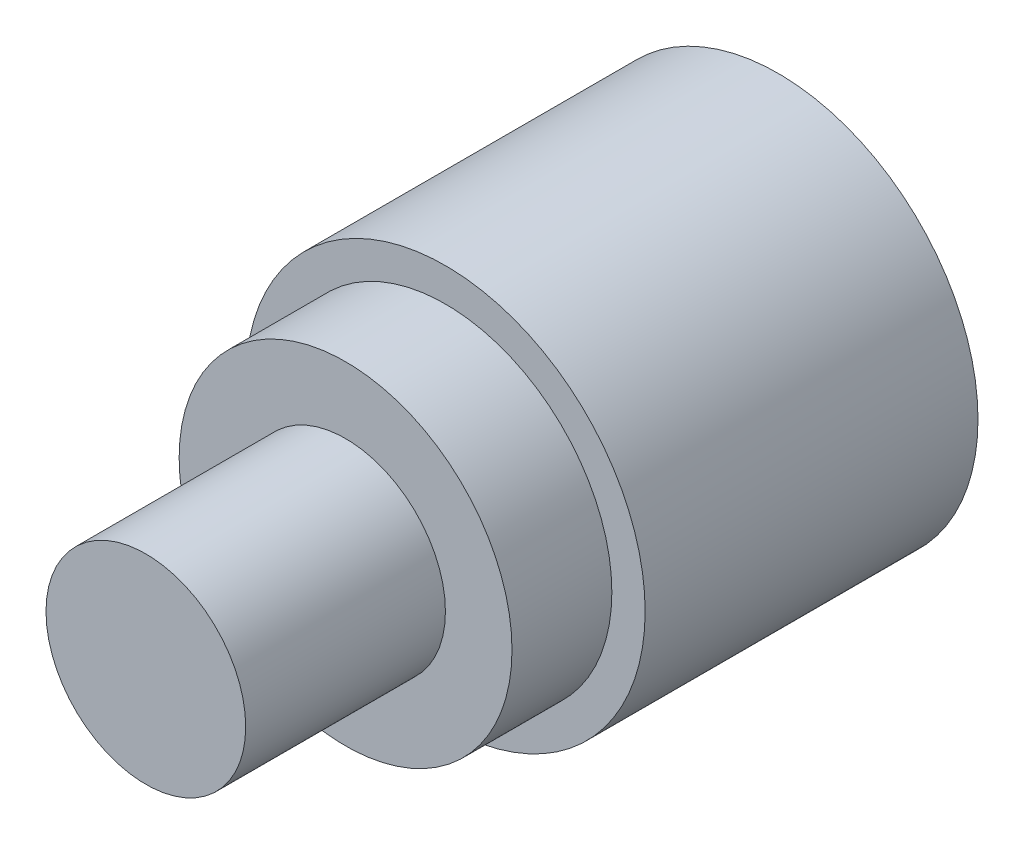
SolidWorks part; units mm, degrees
ref_plane "前视基准面" through (0, 0, 0) normal (0, 0, 1) x (1, 0, 0)
ref_plane "上视基准面" through (0, 0, 0) normal (0, 1, 0) x (1, 0, 0)
ref_plane "右视基准面" through (0, 0, 0) normal (1, 0, 0) x (0, 0, -1)
sketch "草图1" plane through (0, 0, 0) normal (0, 0, 1) x (1, 0, 0)
  circle A0 centre (0, 0) radius 30
  dimension "D1" = 60
extrude "凸台-拉伸1" add sketch "草图1" along normal mid plane 50
sketch "草图3" plane through (0, 0, 25) normal (0, 0, 1) x (1, 0, 0)
  circle A0 centre (0, 0) radius 25
  dimension "D1" = 50
extrude "凸台-拉伸2" add sketch "草图3" along normal blind 15
sketch "草图4" plane through (0, 0, 40) normal (0, 0, 1) x (1, 0, 0)
  circle A0 centre (0, 0) radius 15
  dimension "D1" = 30
extrude "凸台-拉伸3" add sketch "草图4" along normal blind 30
